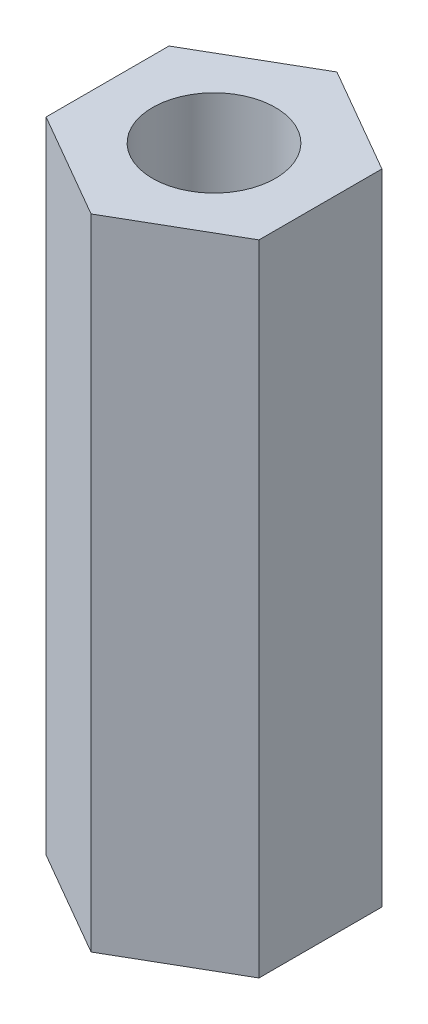
SolidWorks part; units mm, degrees
ref_plane "Face" through (0, 0, 0) normal (0, 0, 1) x (1, 0, 0)
ref_plane "Dessus" through (0, 0, 0) normal (0, 1, 0) x (1, 0, 0)
ref_plane "Droite" through (0, 0, 0) normal (1, 0, 0) x (0, 0, -1)
sketch "Esquisse1" plane through (0, 0, 0) normal (0, 1, 0) x (1, 0, 0)
  line L0 (0, 0) -> (0, 5.5688) construction
  line L1 (0, 5) -> (-4.3301, 2.5)
  line L2 (-4.3301, 2.5) -> (-4.3301, -2.5)
  line L3 (-4.3301, -2.5) -> (0, -5)
  line L4 (0, -5) -> (4.3301, -2.5)
  line L5 (4.3301, -2.5) -> (4.3301, 2.5)
  line L6 (4.3301, 2.5) -> (0, 5)
  circle A0 centre (0, 0) radius 4.3301 construction
  circle A1 centre (0, 0) radius 2.5
  dimension "D1" = 10
  dimension "D2" = 5
extrude "Extrusion1" add sketch "Esquisse1" along normal blind 26
